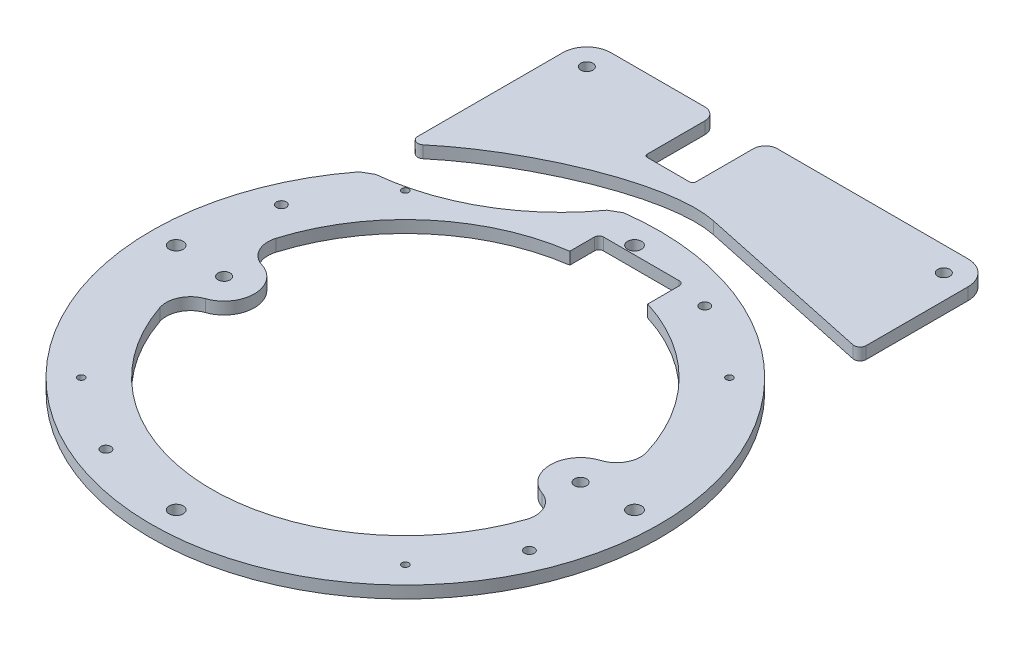
SolidWorks part; units mm, degrees
material "Acrylic (Medium-high impact)"
ref_plane "Front Plane" through (0, 0, 0) normal (0, 0, 1) x (1, 0, 0)
ref_plane "Top Plane" through (0, 0, 0) normal (0, 1, 0) x (1, 0, 0)
ref_plane "Right Plane" through (0, 0, 0) normal (1, 0, 0) x (0, 0, -1)
sketch "Sketch1" plane through (0, 0, 0) normal (0, 1, 0) x (1, 0, 0)
  circle A0 centre (0, 0) radius 133.35
  dimension "D1" = 266.7
extrude "Boss-Extrude1" add sketch "Sketch1" along normal blind 19.05
sketch "Sketch2" plane through (0, 19.05, 0) normal (0, 1, 0) x (1, 0, 0)
  line L0 (-120.2563, 0) -> (120.2563, 0) construction
  line L1 (85.034, 85.034) -> (-85.034, -85.034) construction
  line L2 (85.034, -85.034) -> (-85.034, 85.034) construction
  line L7 (0, 120.2563) -> (0, -120.2563) construction
  line L8 (46.0201, 0) -> (46.0201, 111.1023) construction
  line L9 (46.0201, 111.1023) -> (0, 111.1023) construction
  line L10 (111.1023, 0) -> (111.1023, -46.0201) construction
  line L11 (111.1023, -46.0201) -> (0, -46.0201) construction
  line L12 (0, -111.1023) -> (-46.0201, -111.1023) construction
  line L13 (-46.0201, -111.1023) -> (-46.0201, 0) construction
  line L14 (-111.1023, 0) -> (-111.1023, 46.0201) construction
  line L15 (-111.1023, 46.0201) -> (0, 46.0201) construction
  circle A0 centre (-120.2563, 0) radius 3.6703
  circle A1 centre (-111.1023, 46.0201) radius 2.5781
  circle A2 centre (120.2563, 0) radius 3.6703
  circle A3 centre (0, -120.2563) radius 3.6703
  circle A4 centre (0, 120.2563) radius 3.6703
  circle A5 centre (111.1023, -46.0201) radius 2.5781
  circle A6 centre (-46.0201, -111.1023) radius 2.5781
  circle A7 centre (46.0201, 111.1023) radius 2.5781
  circle A8 centre (-85.034, -85.034) radius 1.7859
  circle A9 centre (85.034, 85.034) radius 1.7859
  circle A10 centre (-85.034, 85.034) radius 1.7859
  circle A11 centre (85.034, -85.034) radius 1.7859
  point P3 (0, 0)
  point P33 (0, 0)
  dimension "D2" = 7.3406
  dimension "D5" = 5.1562
  dimension "D7" = 3.5719
  dimension "D1" = 240.5126
  dimension "D3" = 46.0201
  dimension "D4" = 111.1023
  dimension "D6" = 45
extrude "Cut-Extrude1" cut sketch "Sketch2" against normal through all
sketch "Sketch3" plane through (0, 19.05, 0) normal (0, 1, 0) x (1, 0, 0)
  line L1 (-106.3625, 80.4316) -> (106.3625, 80.4316) construction
  line L2 (-106.3625, 80.4316) -> (-106.3625, 188.9125)
  line L3 (-93.6625, 201.6125) -> (93.6625, 201.6125)
  line L4 (106.3625, 80.4316) -> (106.3625, 188.9125)
  line L5 (-38.1, 201.6125) -> (-106.3625, 201.6125) construction
  circle A0 centre (0, 0) radius 133.35 construction
  arc A1 (106.3625, 80.4316) -> (-106.3625, 80.4316) centre (0, 0) ccw
  arc A2 (-106.3625, 188.9125) -> (-93.6625, 201.6125) centre (-93.6625, 188.9125) cw
  arc A3 (93.6625, 201.6125) -> (106.3625, 188.9125) centre (93.6625, 188.9125) cw
  dimension "D3" = 12.7
  dimension "D1" = 212.725
extrude "Boss-Extrude2" add sketch "Sketch3" against normal up to surface (19.05 mm away) up to face at (0, 0, -116.586)
fillet "Fillet1" radius 25.4 2 edges at (-106.3625, 9.525, -80.4316) (106.3625, 9.525, -80.4316)
sketch "Sketch4" plane through (0, 19.05, 0) normal (0, 1, 0) x (1, 0, 0)
  line L0 (-14.2875, 163.5125) -> (-36.5125, 163.5125) construction
  line L2 (-38.1, 165.1) -> (-38.1, 195.2625) construction
  line L3 (-12.7, 195.2625) -> (-12.7, 165.1) construction
  line L4 (93.6625, 201.6125) -> (-93.6625, 201.6125) construction
  line L5 (-38.1, 165.1) -> (-38.1, 195.2625)
  line L6 (-12.7, 195.2625) -> (-12.7, 165.1)
  line L7 (-14.2875, 163.5125) -> (-36.5125, 163.5125)
  line L8 (-44.45, 201.6125) -> (-6.35, 201.6125)
  circle A0 centre (-93.6625, 188.9125) radius 3.175
  circle A1 centre (93.6625, 188.9125) radius 3.175
  circle A2 centre (93.5355, -1.5875) radius 3.175
  circle A3 centre (-93.5355, -1.5875) radius 3.175
  circle A4 centre (93.5355, -1.5875) radius 3.175 construction
  circle A5 centre (-93.5355, -1.5875) radius 3.175 construction
  arc A6 (-38.1, 165.1) -> (-36.5125, 163.5125) centre (-36.5125, 165.1) ccw construction
  arc A9 (-14.2875, 163.5125) -> (-12.7, 165.1) centre (-14.2875, 165.1) ccw construction
  arc A10 (-38.1, 195.2625) -> (-44.45, 201.6125) centre (-44.45, 195.2625) ccw
  arc A11 (-6.35, 201.6125) -> (-12.7, 195.2625) centre (-6.35, 195.2625) ccw
  arc A12 (-14.2875, 163.5125) -> (-12.7, 165.1) centre (-14.2875, 165.1) ccw
  arc A13 (-38.1, 165.1) -> (-36.5125, 163.5125) centre (-36.5125, 165.1) ccw
  dimension "D1" = 6.35
extrude "Cut-Extrude2" cut sketch "Sketch4" against normal through all
sketch "Sketch5" plane through (0, 0, 0) normal (0, -1, 0) x (1, 0, 0)
  circle A0 centre (-93.5355, 1.5875) radius 7.9375
  circle A2 centre (-93.6625, -188.9125) radius 7.9375
  circle A3 centre (93.6625, -188.9125) radius 7.9375
  circle A5 centre (93.5355, 1.5875) radius 7.9375
  dimension "D1" = 15.875
extrude "Cut-Extrude3" cut sketch "Sketch5" against normal blind 12.7
sketch "Sketch6" plane through (0, 0, 0) normal (0, -1, 0) x (1, 0, 0)
  arc A0 (-97.2571, -29.3874) -> (97.2571, -29.3874) centre (0, 0) ccw
  arc A1 (-88.8491, -13.58) -> (-88.3371, 16.5872) centre (-93.5355, 1.5875) ccw
  arc A2 (97.2571, -29.3874) -> (88.8491, -13.58) centre (85.0999, -25.714) ccw
  arc A3 (88.3371, 16.5872) -> (88.8491, -13.58) centre (93.5355, 1.5875) ccw
  circle A4 centre (-93.5355, 1.5875) radius 7.9375 construction
  arc A5 (-96.2038, 32.6709) -> (-88.3371, 16.5872) centre (-84.1783, 28.587) ccw
  arc A6 (-88.8491, -13.58) -> (-97.2571, -29.3874) centre (-85.0999, -25.714) ccw
  arc A7 (88.3371, 16.5872) -> (96.2038, 32.6709) centre (84.1783, 28.587) ccw
  arc A8 (96.2038, 32.6709) -> (-96.2038, 32.6709) centre (0, 0) ccw
  circle A9 centre (0, -120.2563) radius 15.875 construction
  circle A10 centre (46.0201, -111.1023) radius 15.875 construction
  circle A11 centre (-93.6625, -188.9125) radius 15.875 construction
  circle A12 centre (93.6625, -188.9125) radius 15.875 construction
  circle A22 centre (-85.034, -85.034) radius 15.875 construction
  circle A23 centre (0, 0) radius 120.65 construction
  dimension "D1" = 203.2
  dimension "D2" = 7.9375
  dimension "D3" = 12.7
  dimension "D4" = 31.75
  dimension "D9" = 19.05
extrude "Cut-Extrude4" cut sketch "Sketch6" against normal through all
sketch "Sketch7" plane through (0, 19.05, 0) normal (0, 1, 0) x (1, 0, 0)
  line L0 (-105.6414, 81.3763) -> (-17.6533, 132.1763) construction
  line L1 (106.3625, 131.5277) -> (9.5861, 152.0982)
  line L2 (106.3625, 88.5449) -> (106.3625, 188.9125) construction
  line L3 (-106.3625, 188.9125) -> (-106.3625, 88.5449) construction
  line L5 (106.3625, 131.5277) -> (110.6805, 74.3777)
  line L7 (-105.6414, 81.3763) -> (-100.1422, 84.5513)
  line L8 (-23.1525, 129.0013) -> (-17.6533, 132.1763)
  line L9 (-106.3625, 105.8328) -> (-110.6805, 74.3777)
  circle A0 centre (0, 0) radius 107.95 construction
  circle A1 centre (0, 0) radius 133.35 construction
  arc A2 (-110.6805, 74.3777) -> (110.6805, 74.3777) centre (0, 0) ccw construction
  arc A3 (110.6805, 74.3777) -> (-17.6533, 132.1763) centre (0, 0) ccw
  arc A4 (-110.6805, 74.3777) -> (-105.6414, 81.3763) centre (0, 0) cw
  arc A7 (-100.1422, 84.5513) -> (-23.1525, 129.0013) centre (-111.1244, 192.4732) ccw
  spline S0 degree 3 poles (9.5861, 152.0982) (-20.2337, 158.4366) (-75.8608, 134.1491) (-106.3625, 105.8328) knots 0 0 0 0 1 1 1 1
  point P23 (-56.8848, 98.5274)
  dimension "D1" = 215.9
  dimension "D2" = 152.4
  dimension "D3" = 78
  dimension "D4" = 57.15
  dimension "D5" = 101.6
  dimension "D6" = 9.525
  dimension "D7" = 88.9
  dimension "D8" = 60
  dimension "D9" = 31.75
extrude "Cut-Extrude5" cut sketch "Sketch7" against normal blind 12.7
fillet "Fillet2" radius 3.175 2 edges at (106.3625, 12.7, -131.5277) (-106.3625, 12.7, -105.8328)
sketch "Sketch8" plane through (0, 19.05, 0) normal (0, 1, 0) x (1, 0, 0)
  line L0 (106.3625, 135.4485) -> (106.3625, 188.9125) construction
  line L1 (27.7812, 115.8875) -> (-11.9062, 115.8875)
  line L2 (30.1625, 113.5063) -> (30.1625, 84.1375)
  line L3 (30.1625, 84.1375) -> (-14.2875, 84.1375)
  line L4 (-14.2875, 113.5063) -> (-14.2875, 84.1375)
  line L5 (93.6625, 201.6125) -> (-6.35, 201.6125) construction
  arc A0 (-11.9062, 115.8875) -> (-14.2875, 113.5063) centre (-11.9063, 113.5063) ccw
  arc A1 (27.7812, 115.8875) -> (30.1625, 113.5063) centre (27.7812, 113.5063) cw
  point P13 (-14.2875, 115.8875)
  point P16 (30.1625, 115.8875)
  dimension "D5" = 2.3813
  dimension "D1" = 76.2
  dimension "D2" = 44.45
  dimension "D3" = 31.75
  dimension "D4" = 85.725
extrude "Cut-Extrude6" cut sketch "Sketch8" against normal blind 6.35
sketch "Sketch9" [suppressed] plane through (0, 19.05, 0) normal (0, 1, 0) x (1, 0, 0)
  line L7 (-44.45, 201.6125) -> (-93.6625, 201.6125)
  line L8 (-38.1, 165.1) -> (-38.1, 195.2625)
  line L9 (-14.2875, 163.5125) -> (-36.5125, 163.5125)
  line L10 (-12.7, 195.2625) -> (-12.7, 165.1)
  line L11 (93.6625, 201.6125) -> (-6.35, 201.6125)
  line L12 (106.3625, 88.5449) -> (106.3625, 188.9125)
  line L13 (-106.3625, 188.9125) -> (-106.3625, 88.5449)
  line L14 (-44.45, 201.6125) -> (-93.6625, 201.6125)
  line L15 (-38.1, 165.1) -> (-38.1, 195.2625)
  line L16 (-14.2875, 163.5125) -> (-36.5125, 163.5125)
  line L17 (-12.7, 195.2625) -> (-12.7, 165.1)
  line L18 (93.6625, 201.6125) -> (-6.35, 201.6125)
  line L19 (106.3625, 88.5449) -> (106.3625, 188.9125)
  line L20 (-106.3625, 188.9125) -> (-106.3625, 88.5449)
  arc A9 (-38.1, 195.2625) -> (-44.45, 201.6125) centre (-44.45, 195.2625) ccw
  arc A10 (-38.1, 165.1) -> (-36.5125, 163.5125) centre (-36.5125, 165.1) ccw
  arc A11 (-14.2875, 163.5125) -> (-12.7, 165.1) centre (-14.2875, 165.1) ccw
  arc A12 (-6.35, 201.6125) -> (-12.7, 195.2625) centre (-6.35, 195.2625) ccw
  arc A13 (106.3625, 188.9125) -> (93.6625, 201.6125) centre (93.6625, 188.9125) ccw
  arc A14 (106.3625, 88.5449) -> (110.6805, 74.3777) centre (131.7625, 88.5449) ccw
  arc A15 (-110.6805, 74.3777) -> (110.6805, 74.3777) centre (0, 0) ccw
  arc A16 (-110.6805, 74.3777) -> (-106.3625, 88.5449) centre (-131.7625, 88.5449) ccw
  arc A17 (-93.6625, 201.6125) -> (-106.3625, 188.9125) centre (-93.6625, 188.9125) ccw
  arc A18 (-38.1, 195.2625) -> (-44.45, 201.6125) centre (-44.45, 195.2625) ccw
  arc A19 (-38.1, 165.1) -> (-36.5125, 163.5125) centre (-36.5125, 165.1) ccw
  arc A20 (-14.2875, 163.5125) -> (-12.7, 165.1) centre (-14.2875, 165.1) ccw
  arc A21 (-6.35, 201.6125) -> (-12.7, 195.2625) centre (-6.35, 195.2625) ccw
  arc A22 (106.3625, 188.9125) -> (93.6625, 201.6125) centre (93.6625, 188.9125) ccw
  arc A23 (106.3625, 88.5449) -> (110.6805, 74.3777) centre (131.7625, 88.5449) ccw
  arc A24 (-110.6805, 74.3777) -> (110.6805, 74.3777) centre (0, 0) ccw
  arc A25 (-110.6805, 74.3777) -> (-106.3625, 88.5449) centre (-131.7625, 88.5449) ccw
  arc A26 (-93.6625, 201.6125) -> (-106.3625, 188.9125) centre (-93.6625, 188.9125) ccw
  dimension "D1" = 0
extrude "Cut-Extrude7" [suppressed] cut sketch "Sketch9" against normal blind 12.7
sketch "Sketch10" plane through (0, 0, 0) normal (0, -1, 0) x (1, 0, 0)
  line L7 (-93.6625, -201.6125) -> (-44.45, -201.6125)
  line L8 (-38.1, -195.2625) -> (-38.1, -165.1)
  line L9 (-36.5125, -163.5125) -> (-14.2875, -163.5125)
  line L10 (-12.7, -165.1) -> (-12.7, -195.2625)
  line L11 (-6.35, -201.6125) -> (93.6625, -201.6125)
  line L12 (106.3625, -188.9125) -> (106.3625, -88.5449)
  line L13 (-106.3625, -88.5449) -> (-106.3625, -188.9125)
  line L14 (-93.6625, -201.6125) -> (-44.45, -201.6125)
  line L15 (-38.1, -195.2625) -> (-38.1, -165.1)
  line L16 (-36.5125, -163.5125) -> (-14.2875, -163.5125)
  line L17 (-12.7, -165.1) -> (-12.7, -195.2625)
  line L18 (-6.35, -201.6125) -> (93.6625, -201.6125)
  line L19 (106.3625, -188.9125) -> (106.3625, -88.5449)
  line L20 (-106.3625, -88.5449) -> (-106.3625, -188.9125)
  arc A9 (-44.45, -201.6125) -> (-38.1, -195.2625) centre (-44.45, -195.2625) ccw
  arc A10 (-36.5125, -163.5125) -> (-38.1, -165.1) centre (-36.5125, -165.1) ccw
  arc A11 (-12.7, -165.1) -> (-14.2875, -163.5125) centre (-14.2875, -165.1) ccw
  arc A12 (-12.7, -195.2625) -> (-6.35, -201.6125) centre (-6.35, -195.2625) ccw
  arc A13 (93.6625, -201.6125) -> (106.3625, -188.9125) centre (93.6625, -188.9125) ccw
  arc A14 (110.6805, -74.3777) -> (106.3625, -88.5449) centre (131.7625, -88.5449) ccw
  arc A15 (110.6805, -74.3777) -> (-110.6805, -74.3777) centre (0, 0) ccw
  arc A16 (-106.3625, -88.5449) -> (-110.6805, -74.3777) centre (-131.7625, -88.5449) ccw
  arc A17 (-106.3625, -188.9125) -> (-93.6625, -201.6125) centre (-93.6625, -188.9125) ccw
  arc A18 (-44.45, -201.6125) -> (-38.1, -195.2625) centre (-44.45, -195.2625) ccw
  arc A19 (-36.5125, -163.5125) -> (-38.1, -165.1) centre (-36.5125, -165.1) ccw
  arc A20 (-12.7, -165.1) -> (-14.2875, -163.5125) centre (-14.2875, -165.1) ccw
  arc A21 (-12.7, -195.2625) -> (-6.35, -201.6125) centre (-6.35, -195.2625) ccw
  arc A22 (93.6625, -201.6125) -> (106.3625, -188.9125) centre (93.6625, -188.9125) ccw
  arc A23 (110.6805, -74.3777) -> (106.3625, -88.5449) centre (131.7625, -88.5449) ccw
  arc A24 (110.6805, -74.3777) -> (-110.6805, -74.3777) centre (0, 0) ccw
  arc A25 (-106.3625, -88.5449) -> (-110.6805, -74.3777) centre (-131.7625, -88.5449) ccw
  arc A26 (-106.3625, -188.9125) -> (-93.6625, -201.6125) centre (-93.6625, -188.9125) ccw
  dimension "D1" = 0
extrude "Cut-Extrude8" cut sketch "Sketch10" against normal blind 12.7
